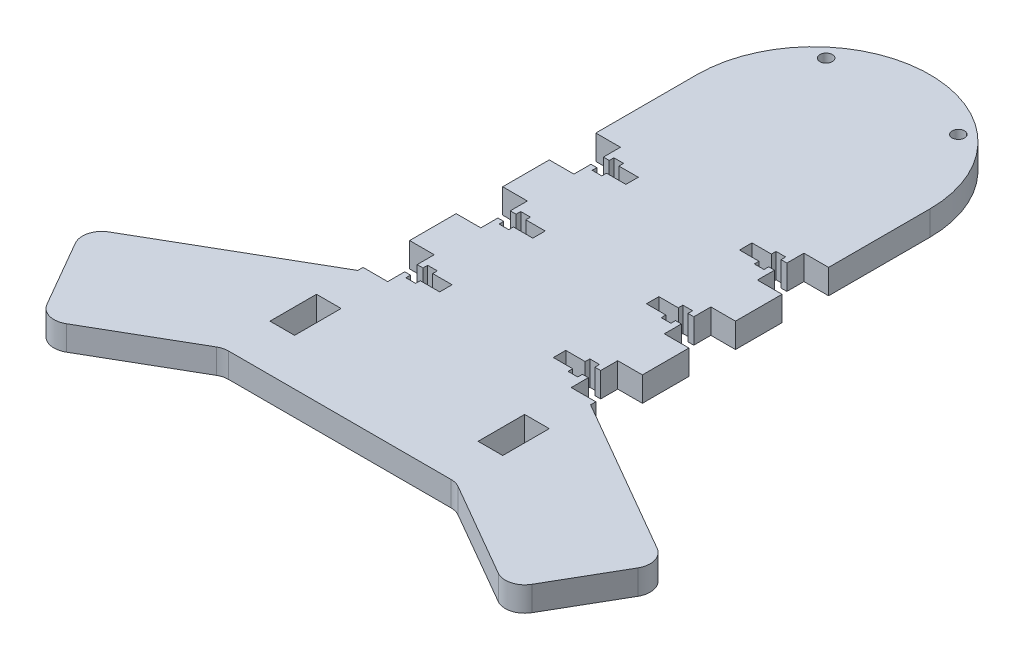
SolidWorks part; units mm, degrees
material "Acrylic (Medium-high impact)"
ref_plane "Front Plane" through (0, 0, 0) normal (0, 0, 1) x (1, 0, 0)
ref_plane "Top Plane" through (0, 0, 0) normal (0, 1, 0) x (1, 0, 0)
ref_plane "Right Plane" through (0, 0, 0) normal (1, 0, 0) x (0, 0, -1)
sketch "Sketch1" plane through (0, 0, 0) normal (0, 1, 0) x (1, 0, 0)
  line L0 (-30, 0) -> (-30, -122.105) construction
  line L1 (-30, -122.105) -> (30, -122.105)
  line L2 (30, -122.105) -> (30, 0) construction
  line L3 (-30, -122.105) -> (-60, -139.4255)
  line L4 (-60, -139.4255) -> (-75, -113.4447)
  line L5 (-75, -113.4447) -> (-30, -87.464)
  line L6 (0, 0) -> (0, -122.105) construction
  line L7 (-30, 0) -> (-30, -87.464)
  line L8 (30, -122.105) -> (60, -139.4255)
  line L9 (60, -139.4255) -> (75, -113.4447)
  line L10 (75, -113.4447) -> (30, -87.464)
  line L11 (30, 0) -> (30, -87.464)
  arc A0 (30, 0) -> (-30, 0) centre (0, 0) ccw
  dimension "D2" = 30
  dimension "D1" = 122.105
  dimension "D4" = 150
  dimension "D5" = 30
  dimension "D6" = 30
extrude "Boss-Extrude1" add sketch "Sketch1" along normal blind 6.35
sketch "Sketch3" plane through (0, 6.35, 0) normal (0, 1, 0) x (1, 0, 0)
  line L0 (-30, 0) -> (-30, -87.464) construction
  line L1 (-30, 0) -> (-30, -87.464) construction
  line L2 (-30, -87.464) -> (-30, -122.105) construction
  line L3 (-30, -122.105) -> (30, -122.105) construction
  line L4 (-30, -98.105) -> (-23.65, -98.105)
  line L5 (-30, -98.105) -> (-30, -110.105)
  line L6 (-30, -110.105) -> (-23.65, -110.105)
  line L7 (-23.65, -98.105) -> (-23.65, -110.105)
  line L8 (-30, -74.105) -> (-30, -86.105)
  line L9 (-30, -74.105) -> (-23.65, -74.105)
  line L10 (-23.65, -74.105) -> (-23.65, -86.105)
  line L11 (-30, -86.105) -> (-23.65, -86.105)
  line L12 (-30, -50.105) -> (-30, -62.105)
  line L13 (-30, -50.105) -> (-23.65, -50.105)
  line L14 (-23.65, -50.105) -> (-23.65, -62.105)
  line L15 (-30, -62.105) -> (-23.65, -62.105)
  line L16 (-30, -26.105) -> (-30, -38.105)
  line L17 (-30, -26.105) -> (-23.65, -26.105)
  line L18 (-23.65, -26.105) -> (-23.65, -38.105)
  line L19 (-30, -38.105) -> (-23.65, -38.105)
  line L20 (0, 0) -> (0, -122.105) construction
  line L21 (30, -38.105) -> (23.65, -38.105)
  line L22 (30, -26.105) -> (30, -38.105)
  line L23 (30, -26.105) -> (23.65, -26.105)
  line L24 (23.65, -26.105) -> (23.65, -38.105)
  line L25 (30, -62.105) -> (23.65, -62.105)
  line L26 (30, -50.105) -> (30, -62.105)
  line L27 (30, -50.105) -> (23.65, -50.105)
  line L28 (23.65, -50.105) -> (23.65, -62.105)
  line L29 (30, -74.105) -> (30, -86.105)
  line L30 (30, -74.105) -> (23.65, -74.105)
  line L31 (23.65, -74.105) -> (23.65, -86.105)
  line L32 (30, -86.105) -> (23.65, -86.105)
  line L33 (30, -98.105) -> (30, -110.105)
  line L34 (30, -98.105) -> (23.65, -98.105)
  line L35 (23.65, -98.105) -> (23.65, -110.105)
  line L36 (30, -110.105) -> (23.65, -110.105)
  dimension "D1" = 12
  dimension "D2" = 12
  dimension "D3" = 6.35
  dimension "D4" = 4
extrude "Cut-Extrude1" cut sketch "Sketch3" against normal up to next
sketch "Sketch4" plane through (0, 6.35, 0) normal (0, 1, 0) x (1, 0, 0)
  line L0 (23.65, -32.105) -> (-23.65, -32.105) construction
  line L1 (23.65, -26.105) -> (23.65, -38.105) construction
  line L2 (-23.65, -38.105) -> (-23.65, -26.105) construction
  line L3 (23.65, -30.505) -> (22.15, -30.505)
  line L4 (22.15, -30.505) -> (22.15, -29.305)
  line L5 (22.15, -29.305) -> (19.65, -29.305)
  line L6 (19.65, -29.305) -> (19.65, -30.505)
  line L7 (19.65, -30.505) -> (14.65, -30.505)
  line L8 (14.65, -30.505) -> (14.65, -33.705)
  line L9 (23.65, -30.505) -> (23.65, -33.705)
  line L10 (23.65, -33.705) -> (22.15, -33.705)
  line L11 (22.15, -33.705) -> (22.15, -34.905)
  line L12 (22.15, -34.905) -> (19.65, -34.905)
  line L13 (19.65, -34.905) -> (19.65, -33.705)
  line L14 (19.65, -33.705) -> (14.65, -33.705)
  line L15 (22.15, -53.305) -> (19.65, -53.305)
  line L16 (19.65, -53.305) -> (19.65, -54.505)
  line L17 (19.65, -54.505) -> (14.65, -54.505)
  line L18 (14.65, -54.505) -> (14.65, -57.705)
  line L19 (19.65, -57.705) -> (14.65, -57.705)
  line L20 (19.65, -58.905) -> (19.65, -57.705)
  line L21 (22.15, -58.905) -> (19.65, -58.905)
  line L22 (22.15, -57.705) -> (22.15, -58.905)
  line L23 (23.65, -57.705) -> (22.15, -57.705)
  line L24 (23.65, -54.505) -> (23.65, -57.705)
  line L25 (23.65, -54.505) -> (22.15, -54.505)
  line L26 (22.15, -54.505) -> (22.15, -53.305)
  line L27 (22.15, -77.305) -> (19.65, -77.305)
  line L28 (19.65, -77.305) -> (19.65, -78.505)
  line L29 (19.65, -78.505) -> (14.65, -78.505)
  line L30 (14.65, -78.505) -> (14.65, -81.705)
  line L31 (19.65, -81.705) -> (14.65, -81.705)
  line L32 (19.65, -82.905) -> (19.65, -81.705)
  line L33 (22.15, -82.905) -> (19.65, -82.905)
  line L34 (22.15, -81.705) -> (22.15, -82.905)
  line L35 (23.65, -81.705) -> (22.15, -81.705)
  line L36 (23.65, -78.505) -> (23.65, -81.705)
  line L37 (23.65, -78.505) -> (22.15, -78.505)
  line L38 (22.15, -78.505) -> (22.15, -77.305)
  line L39 (0, 0) -> (0, -32.105) construction
  line L40 (-22.15, -78.505) -> (-22.15, -77.305)
  line L41 (-23.65, -78.505) -> (-22.15, -78.505)
  line L42 (-23.65, -78.505) -> (-23.65, -81.705)
  line L43 (-23.65, -81.705) -> (-22.15, -81.705)
  line L44 (-22.15, -81.705) -> (-22.15, -82.905)
  line L45 (-22.15, -82.905) -> (-19.65, -82.905)
  line L46 (-19.65, -82.905) -> (-19.65, -81.705)
  line L47 (-19.65, -81.705) -> (-14.65, -81.705)
  line L48 (-14.65, -78.505) -> (-14.65, -81.705)
  line L49 (-19.65, -78.505) -> (-14.65, -78.505)
  line L50 (-19.65, -77.305) -> (-19.65, -78.505)
  line L51 (-22.15, -77.305) -> (-19.65, -77.305)
  line L52 (-22.15, -54.505) -> (-22.15, -53.305)
  line L53 (-23.65, -54.505) -> (-22.15, -54.505)
  line L54 (-23.65, -54.505) -> (-23.65, -57.705)
  line L55 (-23.65, -57.705) -> (-22.15, -57.705)
  line L56 (-22.15, -57.705) -> (-22.15, -58.905)
  line L57 (-22.15, -58.905) -> (-19.65, -58.905)
  line L58 (-19.65, -58.905) -> (-19.65, -57.705)
  line L59 (-19.65, -57.705) -> (-14.65, -57.705)
  line L60 (-14.65, -54.505) -> (-14.65, -57.705)
  line L61 (-19.65, -54.505) -> (-14.65, -54.505)
  line L62 (-19.65, -53.305) -> (-19.65, -54.505)
  line L63 (-22.15, -53.305) -> (-19.65, -53.305)
  line L64 (-19.65, -33.705) -> (-14.65, -33.705)
  line L65 (-19.65, -34.905) -> (-19.65, -33.705)
  line L66 (-22.15, -34.905) -> (-19.65, -34.905)
  line L67 (-22.15, -33.705) -> (-22.15, -34.905)
  line L68 (-23.65, -33.705) -> (-22.15, -33.705)
  line L69 (-23.65, -30.505) -> (-23.65, -33.705)
  line L70 (-14.65, -30.505) -> (-14.65, -33.705)
  line L71 (-19.65, -30.505) -> (-14.65, -30.505)
  line L72 (-19.65, -29.305) -> (-19.65, -30.505)
  line L73 (-22.15, -29.305) -> (-19.65, -29.305)
  line L74 (-22.15, -30.505) -> (-22.15, -29.305)
  line L75 (-23.65, -30.505) -> (-22.15, -30.505)
  point P19 (14.65, -32.105)
  point P83 (-14.65, -32.105)
  dimension "D1" = 1.6
  dimension "D2" = 2.8
  dimension "D3" = 2.5
  dimension "D4" = 1.5
  dimension "D5" = 9
  dimension "D7" = 24
  dimension "D6" = 3
extrude "Cut-Extrude2" cut sketch "Sketch4" against normal up to next
sketch "Sketch5" plane through (0, 6.35, 0) normal (0, 1, 0) x (1, 0, 0)
  line L0 (0, 0) -> (0, 30) construction
  line L1 (0, 0) -> (-17.0339, 20.3002) construction
  arc A0 (30, 0) -> (-30, 0) centre (0, 0) ccw construction
  circle A1 centre (-17.0339, 20.3002) radius 1.6
  circle A2 centre (17.0339, 20.3002) radius 1.6
  dimension "D3" = 3.2
  dimension "D1" = 26.5
  dimension "D2" = 40
extrude "Cut-Extrude3" cut sketch "Sketch5" against normal through all
fillet "Fillet1" radius 5 6 edges at (-30, 3.175, 122.105) (30, 3.175, 122.105) (60, 3.175, 139.4255) (75, 3.175, 113.4447) (-60, 3.175, 139.4255) (-75, 3.175, 113.4447)
